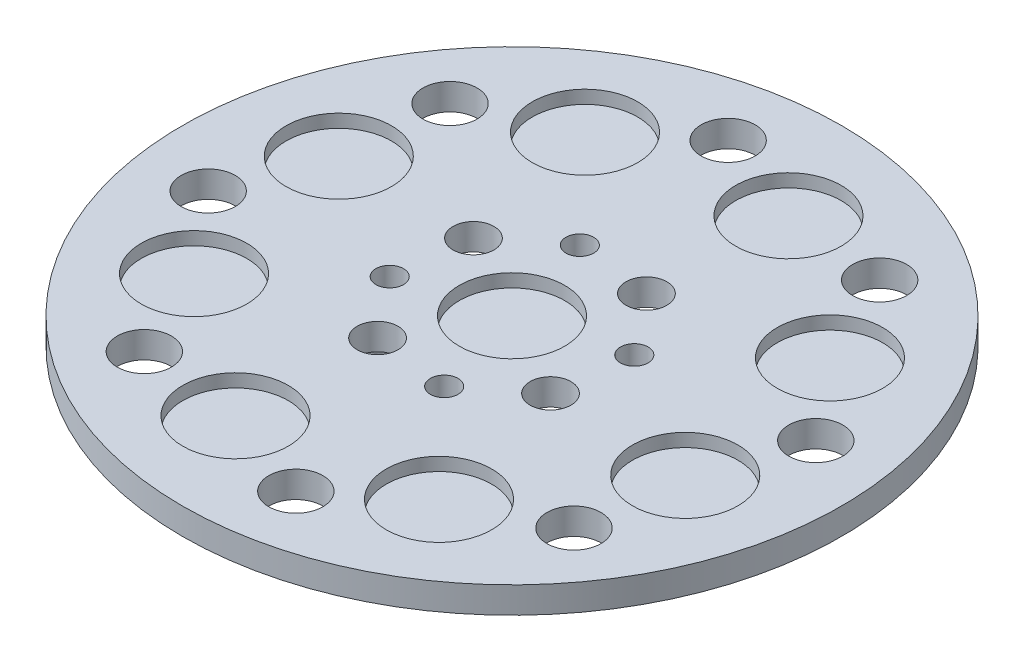
SolidWorks part; units mm, degrees
material "Plain Carbon Steel"
ref_plane "Front Plane" through (0, 0, 0) normal (0, 0, 1) x (1, 0, 0)
ref_plane "Top Plane" through (0, 0, 0) normal (0, 1, 0) x (1, 0, 0)
ref_plane "Right Plane" through (0, 0, 0) normal (1, 0, 0) x (0, 0, -1)
sketch "Sketch1" plane through (0, 0, 0) normal (0, 1, 0) x (1, 0, 0)
  circle A0 centre (0, 0) radius 25
  dimension "D1" = 50
extrude "Boss-Extrude1" add sketch "Sketch1" along normal blind 2
sketch "Sketch2" plane through (0, 2, 0) normal (0, 1, 0) x (1, 0, 0)
  circle A0 centre (0, 0) radius 7.5 construction
  circle A1 centre (-2.0664, 7.2097) radius 1.05
  circle A2 centre (7.2097, 2.0664) radius 1.05
  circle A3 centre (2.0664, -7.2097) radius 1.05
  circle A4 centre (-7.2097, -2.0664) radius 1.05
  point P21 (0, 0)
  dimension "D1" = 15
  dimension "D2" = 2.1
  dimension "D3" = 4
extrude "Cut-Extrude1" cut sketch "Sketch2" against normal through all
sketch "Sketch3" plane through (0, 2, 0) normal (0, 1, 0) x (1, 0, 0)
  circle A0 centre (0, 0) radius 4
  circle A1 centre (0, 0) radius 17.5 construction
  circle A2 centre (17.0562, -3.9161) radius 4
  circle A3 centre (9.2915, -14.8296) radius 4
  circle A4 centre (-3.9161, -17.0562) radius 4
  circle A5 centre (-14.8296, -9.2915) radius 4
  circle A6 centre (-17.0562, 3.9161) radius 4
  circle A7 centre (-9.2915, 14.8296) radius 4
  circle A8 centre (3.9161, 17.0562) radius 4
  circle A9 centre (14.8296, 9.2915) radius 4
  point P23 (0, 0)
  dimension "D1" = 35
  dimension "8" = 8
  dimension "D2" = 8
  dimension "D3" = 8
extrude "Cut-Extrude2" cut sketch "Sketch3" against normal blind 1
sketch "Sketch4" plane through (0, 0, 0) normal (0, -1, 0) x (1, 0, 0)
  circle A0 centre (0, 0) radius 7.5 construction
  circle A1 centre (2.0664, 7.2097) radius 3
  circle A4 centre (2.0664, 7.2097) radius 1.95
  circle A11 centre (7.2097, -2.0664) radius 1.95
  circle A12 centre (7.2097, -2.0664) radius 3
  circle A13 centre (-2.0664, -7.2097) radius 1.95
  circle A14 centre (-2.0664, -7.2097) radius 3
  circle A15 centre (-7.2097, 2.0664) radius 1.95
  circle A16 centre (-7.2097, 2.0664) radius 3
  point P19 (0, 0)
  point P21 (-7.2097, 2.0664)
  dimension "D1" = 6
  dimension "D2" = 3.9
  dimension "D3" = 4
extrude "Boss-Extrude2" add sketch "Sketch4" along normal blind 6
fillet "Fillet1" radius 1 4 edges at (2.0664, 0, 10.2097) (-7.2097, 0, 5.0664) (-2.0664, 0, -4.2097) (7.2097, 0, 0.9336)
sketch "Sketch5" plane through (0, 2, 0) normal (0, 1, 0) x (1, 0, 0)
  line L0 (0, 0) -> (-11.5944, -16.2963) construction
  line L2 (0, 0) -> (-3.9161, -17.0562) construction
  line L3 (0, 0) -> (-14.8296, -9.2915) construction
  circle A0 centre (0, 0) radius 20 construction
  circle A1 centre (-11.5944, -16.2963) radius 2.05
  circle A2 centre (-19.7217, -3.3248) radius 2.05
  circle A3 centre (-16.2963, 11.5944) radius 2.05
  circle A4 centre (-3.3248, 19.7217) radius 2.05
  circle A5 centre (11.5944, 16.2963) radius 2.05
  circle A6 centre (19.7217, 3.3248) radius 2.05
  circle A7 centre (16.2963, -11.5944) radius 2.05
  circle A8 centre (3.3248, -19.7217) radius 2.05
  point P26 (0, 0)
  dimension "D1" = 40
  dimension "D4" = 4.1
  dimension "D2" = 45
  dimension "D3" = 22.5
  dimension "D5" = 8
extrude "Cut-Extrude3" cut sketch "Sketch5" against normal through all contours A1
sketch "Sketch7" plane through (0, 2, -2) normal (0, -1, 0) x (1, 0, 0)
  line L0 (7.2097, -0.0664) -> (-7.2097, 4.0664) construction
  line L1 (0, 2) -> (-5.6855, 12.2539) construction
  circle A0 centre (0, 2) radius 7.5 construction
  circle A1 centre (-3.6369, 8.5592) radius 1.55
  circle A7 centre (6.5592, 5.6369) radius 1.55
  circle A8 centre (3.6369, -4.5592) radius 1.55
  circle A9 centre (-6.5592, -1.6369) radius 1.55
  point P17 (0, 2)
  point P21 (0, 0)
  dimension "D1" = 15
  dimension "D2" = 3.1
  dimension "D4" = 45
  dimension "D3" = 4
extrude "Cut-Extrude4" cut sketch "Sketch7" along normal through all contours A8 | A7 | A1 | A9
equation "\"D3@Sketch5\"=\"D2@Sketch5\"/2"
